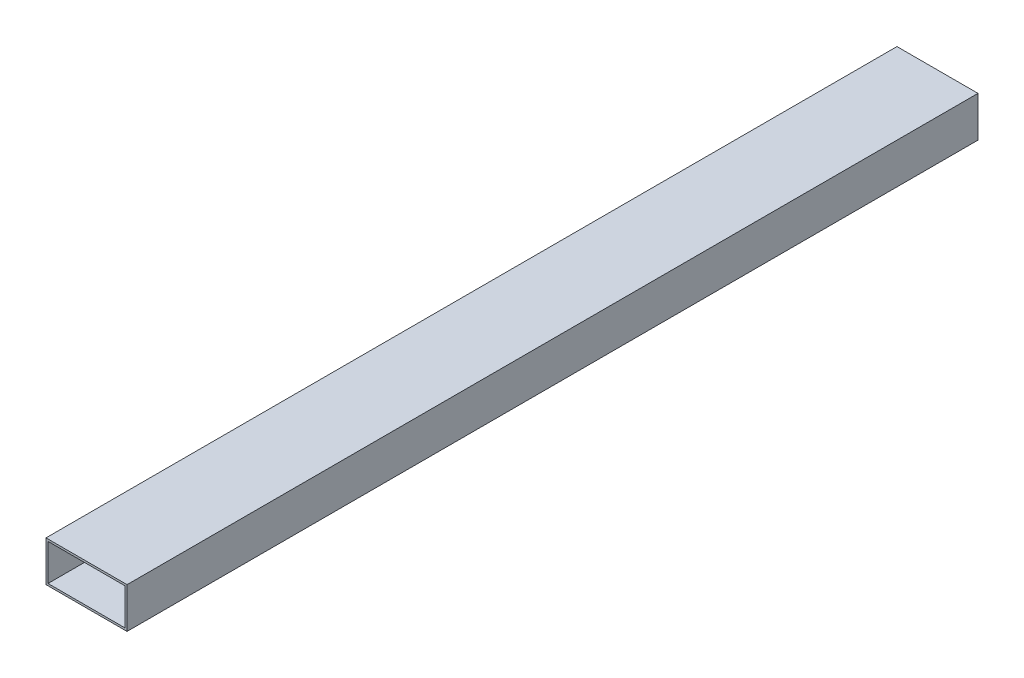
SolidWorks part; units mm, degrees
ref_plane "Front Plane" through (0, 0, 0) normal (0, 0, 1) x (1, 0, 0)
ref_plane "Top Plane" through (0, 0, 0) normal (0, 1, 0) x (1, 0, 0)
ref_plane "Right Plane" through (0, 0, 0) normal (1, 0, 0) x (0, 0, -1)
sketch "Sketch1" plane through (0, 0, 0) normal (0, 0, 1) x (1, 0, 0)
  line L0 (0, 11.5123) -> (0, -11.9084) construction
  line L1 (25.9837, 0) -> (-26.974, 0) construction
  line L2 (-20, 10) -> (20, 10)
  line L3 (20, 10) -> (20, -10)
  line L4 (20, -10) -> (-20, -10)
  line L5 (-20, -10) -> (-20, 10)
  point P7 (0, 10)
  point P10 (20, 0)
  point P11 (-20, 0)
  dimension "D1" = 40
  dimension "D2" = 20
extrude "Boss-Extrude1" add sketch "Sketch1" along normal blind 420
sketch "Sketch2" plane through (0, 0, 420) normal (0, 0, 1) x (1, 0, 0)
  line L8 (-19, 9) -> (-19, -9)
  line L9 (-19, -9) -> (19, -9)
  line L10 (19, -9) -> (19, 9)
  line L11 (19, 9) -> (-19, 9)
  line L12 (-19, 9) -> (-19, -9)
  line L13 (-19, -9) -> (19, -9)
  line L14 (19, -9) -> (19, 9)
  line L15 (19, 9) -> (-19, 9)
  dimension "D1" = 1
extrude "Cut-Extrude1" cut sketch "Sketch2" against normal through all
